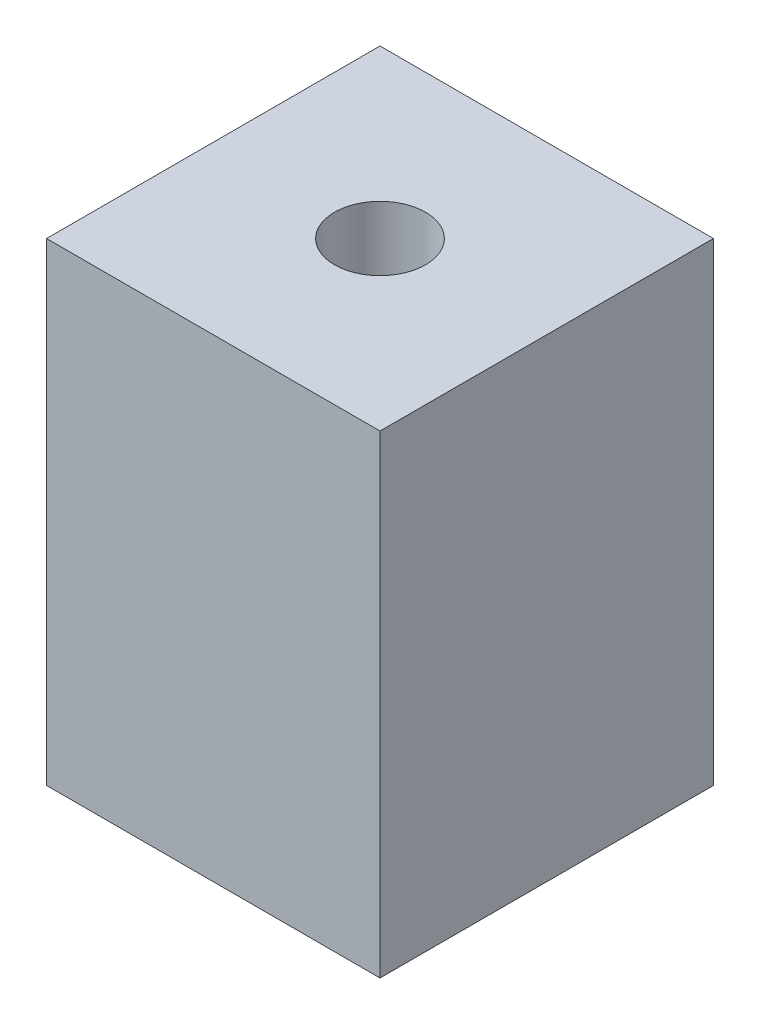
SolidWorks part; units mm, degrees
ref_plane "Front Plane" through (0, 0, 0) normal (0, 0, 1) x (1, 0, 0)
ref_plane "Top Plane" through (0, 0, 0) normal (0, 1, 0) x (1, 0, 0)
ref_plane "Right Plane" through (0, 0, 0) normal (1, 0, 0) x (0, 0, -1)
sketch "Sketch2" plane through (0, 0, 0) normal (0, 1, 0) x (1, 0, 0)
  line L1 (-23.241, 23.241) -> (23.241, 23.241)
  line L2 (-23.241, 23.241) -> (-23.241, -23.241)
  line L3 (-23.241, -23.241) -> (23.241, -23.241)
  line L4 (23.241, 23.241) -> (23.241, -23.241)
  line L5 (-23.241, 23.241) -> (23.241, -23.241) construction
  line L6 (-23.241, -23.241) -> (23.241, 23.241) construction
  point P0 (0, 0)
  dimension "D1" = 46.482
extrude "Boss-Extrude1" add sketch "Sketch2" along normal blind 66.04
sketch "Sketch3" plane through (0, 66.04, 0) normal (0, 1, 0) x (1, 0, 0)
  circle A0 centre (0, 0) radius 6.35
  dimension "D1" = 12.7
extrude "Cut-Extrude1" cut sketch "Sketch3" against normal blind 12.7
sketch "Sketch4" plane through (0, 0, 0) normal (0, -1, 0) x (1, 0, 0)
  circle A0 centre (0, 0) radius 6.35
  dimension "D1" = 12.7
extrude "Cut-Extrude2" cut sketch "Sketch4" against normal blind 12.7
